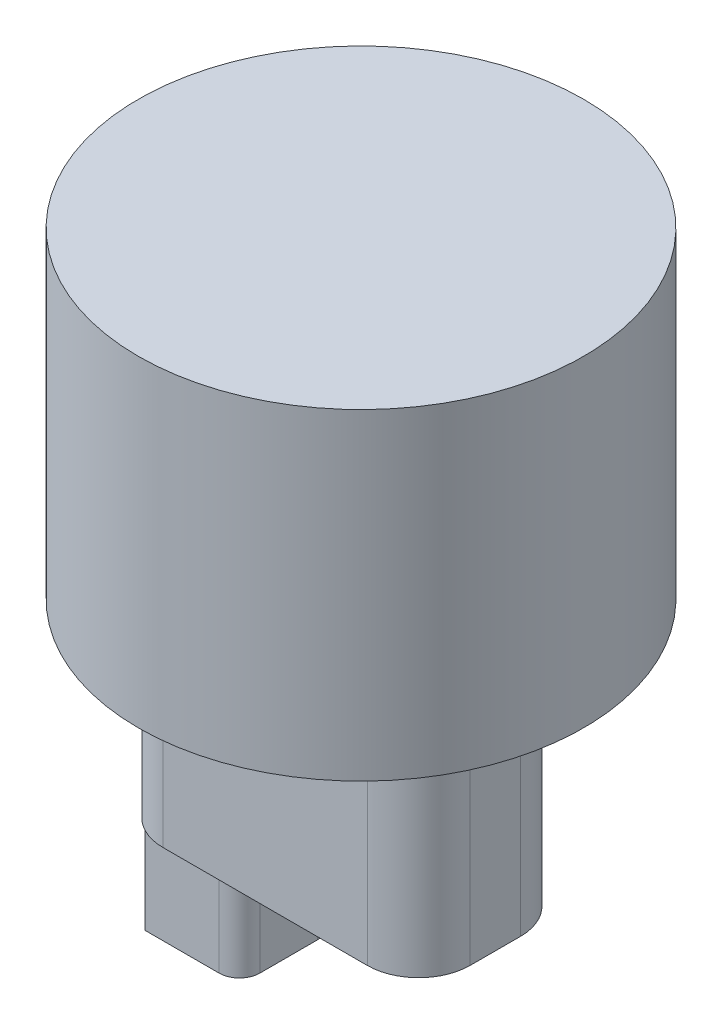
SolidWorks part; units mm, degrees
ref_plane "Front Plane" through (0, 0, 0) normal (0, 0, 1) x (1, 0, 0)
ref_plane "Top Plane" through (0, 0, 0) normal (0, 1, 0) x (1, 0, 0)
ref_plane "Right Plane" through (0, 0, 0) normal (1, 0, 0) x (0, 0, -1)
sketch "Sketch1" plane through (0, 0, 0) normal (0, 1, 0) x (1, 0, 0)
  circle A0 centre (0, 0) radius 58
  dimension "D1" = 116
extrude "Boss-Extrude1" add sketch "Sketch1" along normal blind 83.82
sketch "Sketch2" plane through (0, 0, 0) normal (0, 1, 0) x (1, 0, 0)
  line L0 (0, 0) -> (-45, 0) construction
  line L1 (-45, -6.5689) -> (-45, 6.5689)
  line L3 (35, 6.5689) -> (35, -6.5689)
  line L5 (-31.6, 19.9689) -> (21.6, 19.9689)
  line L6 (-31.6, -19.9689) -> (21.6, -19.9689)
  arc A0 (-45, 6.5689) -> (-31.6, 19.9689) centre (-31.6, 6.5689) cw
  arc A1 (-31.6, -19.9689) -> (-45, -6.5689) centre (-31.6, -6.5689) cw
  arc A2 (21.6, 19.9689) -> (35, 6.5689) centre (21.6, 6.5689) cw
  arc A3 (21.6, -19.9689) -> (35, -6.5689) centre (21.6, -6.5689) ccw
  point P7 (35, 0)
  point P10 (-45, 19.9689)
  point P13 (-45, -19.9689)
  point P16 (35, 19.9689)
  point P19 (35, -19.9689)
  dimension "D3" = 13.4
  dimension "D1" = 13.4
  dimension "D2" = 13.4
  dimension "D4" = 13.4
extrude "Boss-Extrude2" add sketch "Sketch2" against normal blind 61.8
sketch "Sketch3" plane through (0, 0, 0) normal (0, 1, 0) x (1, 0, 0)
  line L0 (-21.5525, -4.8) -> (-21.5525, 4.8)
  line L1 (-26.8525, -10.1) -> (-44.5264, -10.1)
  line L2 (-26.8525, 10.1) -> (-44.5264, 10.1)
  line L3 (-21.5525, 0) -> (-18.8525, 0) construction
  line L4 (-18.8525, 7.5) -> (-18.8525, -7.5)
  line L5 (-45, 0) -> (-14.5512, 0) construction
  line L6 (-45, 6.5689) -> (-45, -6.5689) construction
  line L7 (-24.1525, -12.8) -> (-40.1892, -12.8)
  line L8 (-40.1892, -12.8) -> (-43.4631, -12.8)
  line L9 (-21.5525, -4.8) -> (-21.5525, -7.4)
  line L10 (-24.2525, -10.1) -> (-26.8525, -10.1)
  line L11 (-24.2525, 10.1) -> (-26.8525, 10.1)
  line L12 (-21.5525, 4.8) -> (-21.5525, 7.4)
  line L13 (-24.1525, 12.8) -> (-43.4631, 12.8)
  line L14 (-43.4631, 12.8) -> (-44.5264, 10.1)
  line L15 (-43.4631, -12.8) -> (-44.5264, -10.1)
  arc A0 (-45, -6.5689) -> (-31.6, -19.9689) centre (-31.6, -6.5689) ccw construction
  arc A1 (-21.5525, -7.4) -> (-24.2525, -10.1) centre (-24.2525, -7.4) cw
  arc A2 (-18.8525, -7.5) -> (-24.1525, -12.8) centre (-24.1525, -7.5) cw
  arc A3 (-18.8525, 7.5) -> (-24.1525, 12.8) centre (-24.1525, 7.5) ccw
  arc A4 (-21.5525, 7.4) -> (-24.2525, 10.1) centre (-24.2525, 7.4) ccw
  arc A5 (-31.6, 19.9689) -> (-45, 6.5689) centre (-31.6, 6.5689) ccw construction
  point P17 (-21.5525, 0)
  point P18 (-21.5525, 0)
  dimension "D1" = 2.7
  dimension "D3" = 10.1
  dimension "D4" = 2.7
  dimension "D6" = 5.3
  dimension "D2" = 4.8
  dimension "D5" = 2.7
extrude "Boss-Extrude3" add sketch "Sketch3" against normal blind 90 contours L15 L1 L10 A1 L9 L0 L12 A4 L11 L2 L14 L13 A3 L4 A2 L7 L8
